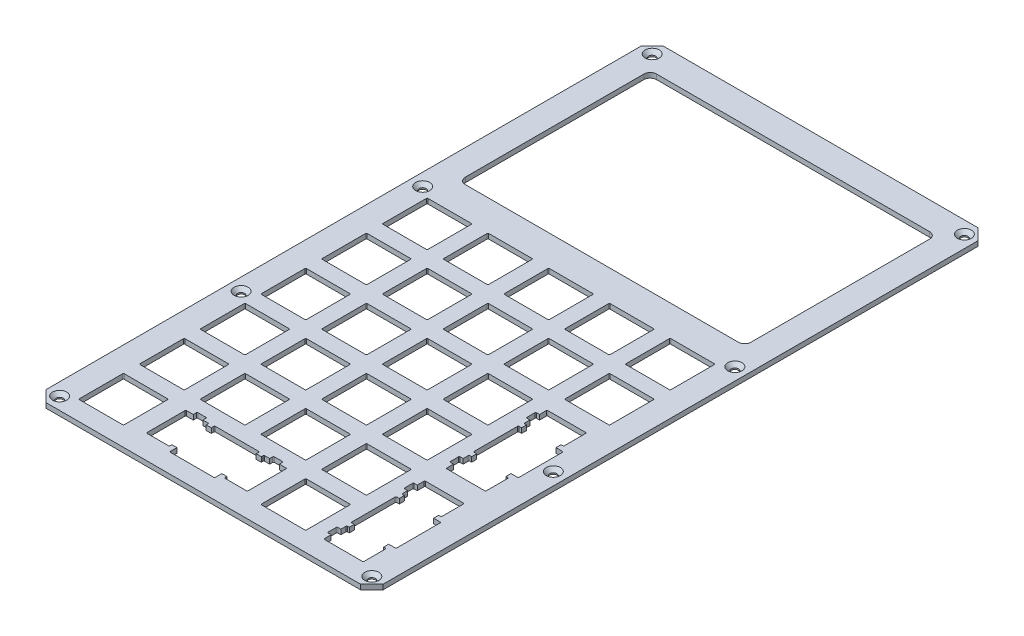
SolidWorks part; units mm, degrees
material "Brass"
ref_plane "Front Plane" through (0, 0, 0) normal (0, 0, 1) x (1, 0, 0)
ref_plane "Top Plane" through (0, 0, 0) normal (0, 1, 0) x (1, 0, 0)
ref_plane "Right Plane" through (0, 0, 0) normal (1, 0, 0) x (0, 0, -1)
sketch "Sketch1" plane through (0, 0, 0) normal (0, 1, 0) x (1, 0, 0)
  line L0 (25.9207, -6.9977) -> (25.9207, 6.9977)
  line L1 (6.9977, -6.9977) -> (-6.9977, -6.9977)
  line L2 (6.9977, -6.9977) -> (6.9977, 6.9977)
  line L3 (6.9977, 6.9977) -> (-6.9977, 6.9977)
  line L4 (-6.9977, -6.9977) -> (-6.9977, 6.9977)
  line L5 (6.9977, -6.9977) -> (-6.9977, 6.9977) construction
  line L6 (6.9977, 6.9977) -> (-6.9977, -6.9977) construction
  line L7 (25.9207, -6.9977) -> (11.9253, -6.9977)
  line L8 (11.9253, -6.9977) -> (11.9253, 6.9977)
  line L9 (25.9207, 6.9977) -> (11.9253, 6.9977)
  line L10 (44.8437, -6.9977) -> (44.8437, 6.9977)
  line L11 (44.8437, -6.9977) -> (30.8483, -6.9977)
  line L12 (30.8483, -6.9977) -> (30.8483, 6.9977)
  line L13 (44.8437, 6.9977) -> (30.8483, 6.9977)
  line L14 (63.7667, -6.9977) -> (63.7667, 6.9977)
  line L15 (63.7667, -6.9977) -> (49.7713, -6.9977)
  line L16 (49.7713, -6.9977) -> (49.7713, 6.9977)
  line L17 (63.7667, 6.9977) -> (49.7713, 6.9977)
  line L18 (82.6897, -6.9977) -> (82.6897, 6.9977)
  line L19 (82.6897, -6.9977) -> (68.6943, -6.9977)
  line L20 (68.6943, -6.9977) -> (68.6943, 6.9977)
  line L21 (82.6897, 6.9977) -> (68.6943, 6.9977)
  line L22 (25.9207, -25.9207) -> (25.9207, -11.9253)
  line L23 (25.9207, -25.9207) -> (11.9253, -25.9207)
  line L24 (11.9253, -25.9207) -> (11.9253, -11.9253)
  line L25 (25.9207, -11.9253) -> (11.9253, -11.9253)
  line L26 (44.8437, -25.9207) -> (44.8437, -11.9253)
  line L27 (44.8437, -25.9207) -> (30.8483, -25.9207)
  line L28 (30.8483, -25.9207) -> (30.8483, -11.9253)
  line L29 (44.8437, -11.9253) -> (30.8483, -11.9253)
  line L30 (63.7667, -25.9207) -> (63.7667, -11.9253)
  line L31 (63.7667, -25.9207) -> (49.7713, -25.9207)
  line L32 (49.7713, -25.9207) -> (49.7713, -11.9253)
  line L33 (63.7667, -11.9253) -> (49.7713, -11.9253)
  line L34 (82.6897, -25.9207) -> (82.6897, -11.9253)
  line L35 (82.6897, -25.9207) -> (68.6943, -25.9207)
  line L36 (68.6943, -25.9207) -> (68.6943, -11.9253)
  line L37 (82.6897, -11.9253) -> (68.6943, -11.9253)
  line L38 (25.9207, -44.8437) -> (25.9207, -30.8483)
  line L39 (25.9207, -44.8437) -> (11.9253, -44.8437)
  line L40 (11.9253, -44.8437) -> (11.9253, -30.8483)
  line L41 (25.9207, -30.8483) -> (11.9253, -30.8483)
  line L42 (44.8437, -44.8437) -> (44.8437, -30.8483)
  line L43 (44.8437, -44.8437) -> (30.8483, -44.8437)
  line L44 (30.8483, -44.8437) -> (30.8483, -30.8483)
  line L45 (44.8437, -30.8483) -> (30.8483, -30.8483)
  line L46 (63.7667, -44.8437) -> (63.7667, -30.8483)
  line L47 (63.7667, -44.8437) -> (49.7713, -44.8437)
  line L48 (49.7713, -44.8437) -> (49.7713, -30.8483)
  line L49 (63.7667, -30.8483) -> (49.7713, -30.8483)
  line L50 (82.6897, -44.8437) -> (82.6897, -30.8483) [skipped]
  line L51 (82.6897, -44.8437) -> (68.6943, -44.8437) [skipped]
  line L52 (68.6943, -44.8437) -> (68.6943, -30.8483) [skipped]
  line L53 (82.6897, -30.8483) -> (68.6943, -30.8483) [skipped]
  line L54 (25.9207, -63.7667) -> (25.9207, -49.7713)
  line L55 (25.9207, -63.7667) -> (11.9253, -63.7667)
  line L56 (11.9253, -63.7667) -> (11.9253, -49.7713)
  line L57 (25.9207, -49.7713) -> (11.9253, -49.7713)
  line L58 (44.8437, -63.7667) -> (44.8437, -49.7713)
  line L59 (44.8437, -63.7667) -> (30.8483, -63.7667)
  line L60 (30.8483, -63.7667) -> (30.8483, -49.7713)
  line L61 (44.8437, -49.7713) -> (30.8483, -49.7713)
  line L62 (63.7667, -63.7667) -> (63.7667, -49.7713)
  line L63 (63.7667, -63.7667) -> (49.7713, -63.7667)
  line L64 (49.7713, -63.7667) -> (49.7713, -49.7713)
  line L65 (63.7667, -49.7713) -> (49.7713, -49.7713)
  line L66 (82.6897, -63.7667) -> (82.6897, -49.7713) [skipped]
  line L67 (82.6897, -63.7667) -> (68.6943, -63.7667) [skipped]
  line L68 (68.6943, -63.7667) -> (68.6943, -49.7713) [skipped]
  line L69 (82.6897, -49.7713) -> (68.6943, -49.7713) [skipped]
  line L70 (25.9207, -82.6897) -> (25.9207, -68.6943)
  line L71 (25.9207, -82.6897) -> (11.9253, -82.6897)
  line L72 (11.9253, -82.6897) -> (11.9253, -68.6943)
  line L73 (25.9207, -68.6943) -> (11.9253, -68.6943)
  line L74 (44.8437, -82.6897) -> (44.8437, -68.6943)
  line L75 (44.8437, -82.6897) -> (30.8483, -82.6897)
  line L76 (30.8483, -82.6897) -> (30.8483, -68.6943)
  line L77 (44.8437, -68.6943) -> (30.8483, -68.6943)
  line L78 (63.7667, -82.6897) -> (63.7667, -68.6943)
  line L79 (63.7667, -82.6897) -> (49.7713, -82.6897)
  line L80 (49.7713, -82.6897) -> (49.7713, -68.6943)
  line L81 (63.7667, -68.6943) -> (49.7713, -68.6943)
  line L82 (82.6897, -82.6897) -> (82.6897, -68.6943) [skipped]
  line L83 (82.6897, -82.6897) -> (68.6943, -82.6897) [skipped]
  line L84 (68.6943, -82.6897) -> (68.6943, -68.6943) [skipped]
  line L85 (82.6897, -68.6943) -> (68.6943, -68.6943) [skipped]
  line L86 (25.9207, -101.6127) -> (25.9207, -87.6173) [skipped]
  line L87 (25.9207, -101.6127) -> (11.9253, -101.6127) [skipped]
  line L88 (11.9253, -101.6127) -> (11.9253, -87.6173) [skipped]
  line L89 (25.9207, -87.6173) -> (11.9253, -87.6173) [skipped]
  line L90 (44.8437, -101.6127) -> (44.8437, -87.6173) [skipped]
  line L91 (44.8437, -101.6127) -> (30.8483, -101.6127) [skipped]
  line L92 (30.8483, -101.6127) -> (30.8483, -87.6173) [skipped]
  line L93 (44.8437, -87.6173) -> (30.8483, -87.6173) [skipped]
  line L94 (63.7667, -101.6127) -> (63.7667, -87.6173)
  line L95 (63.7667, -101.6127) -> (49.7713, -101.6127)
  line L96 (49.7713, -101.6127) -> (49.7713, -87.6173)
  line L97 (63.7667, -87.6173) -> (49.7713, -87.6173)
  line L98 (82.6897, -101.6127) -> (82.6897, -87.6173) [skipped]
  line L99 (82.6897, -101.6127) -> (68.6943, -101.6127) [skipped]
  line L100 (68.6943, -101.6127) -> (68.6943, -87.6173) [skipped]
  line L101 (82.6897, -87.6173) -> (68.6943, -87.6173) [skipped]
  line L102 (6.9977, -25.9207) -> (6.9977, -11.9253)
  line L103 (6.9977, -25.9207) -> (-6.9977, -25.9207)
  line L104 (-6.9977, -25.9207) -> (-6.9977, -11.9253)
  line L105 (6.9977, -11.9253) -> (-6.9977, -11.9253)
  line L106 (6.9977, -44.8437) -> (6.9977, -30.8483)
  line L107 (6.9977, -44.8437) -> (-6.9977, -44.8437)
  line L108 (-6.9977, -44.8437) -> (-6.9977, -30.8483)
  line L109 (6.9977, -30.8483) -> (-6.9977, -30.8483)
  line L110 (6.9977, -63.7667) -> (6.9977, -49.7713)
  line L111 (6.9977, -63.7667) -> (-6.9977, -63.7667)
  line L112 (-6.9977, -63.7667) -> (-6.9977, -49.7713)
  line L113 (6.9977, -49.7713) -> (-6.9977, -49.7713)
  line L114 (6.9977, -82.6897) -> (6.9977, -68.6943)
  line L115 (6.9977, -82.6897) -> (-6.9977, -82.6897)
  line L116 (-6.9977, -82.6897) -> (-6.9977, -68.6943)
  line L117 (6.9977, -68.6943) -> (-6.9977, -68.6943)
  line L118 (6.9977, -101.6127) -> (6.9977, -87.6173)
  line L119 (6.9977, -101.6127) -> (-6.9977, -101.6127)
  line L120 (-6.9977, -101.6127) -> (-6.9977, -87.6173)
  line L121 (6.9977, -87.6173) -> (-6.9977, -87.6173)
  line L122 (6.9977, -6.9977) -> (25.9207, -6.9977) construction
  line L123 (6.9977, -6.9977) -> (6.9977, -25.9207) construction
  line L124 (25.9207, -75.692) -> (30.8483, -75.692) construction
  line L125 (56.769, -44.8437) -> (56.769, -49.7713) construction
  line L126 (13.1595, -100.1473) -> (12.6515, -100.1473)
  line L127 (-14.654, 84.7537) -> (90.346, 84.7537)
  line L128 (-14.654, 84.7537) -> (-14.654, -107.5917)
  line L129 (-14.654, -107.5917) -> (90.346, -107.5917)
  line L130 (90.346, 84.7537) -> (90.346, -107.5917)
  line L131 (82.3656, 76.1637) -> (-6.6736, 76.1637)
  line L132 (82.3656, 76.1637) -> (82.3656, 16.5377)
  line L133 (82.3656, 16.5377) -> (-6.6736, 16.5377)
  line L134 (-6.6736, 76.1637) -> (-6.6736, 16.5377)
  line L135 (82.3656, 76.1637) -> (-6.6736, 16.5377) construction
  line L136 (82.3656, 16.5377) -> (-6.6736, 76.1637) construction
  line L137 (12.6515, -100.1473) -> (12.6515, -87.8473)
  line L138 (12.6515, -87.8473) -> (13.1595, -87.8473)
  line L139 (43.6095, -87.8473) -> (44.1175, -87.8473)
  line L140 (44.1175, -87.8473) -> (44.1175, -100.1473)
  line L141 (44.1175, -100.1473) -> (43.6095, -100.1473)
  line L142 (68.9243, -100.6325) -> (68.9243, -101.1405)
  line L143 (68.9243, -101.1405) -> (81.2243, -101.1405)
  line L144 (81.2243, -101.1405) -> (81.2243, -100.6325)
  line L145 (68.9243, -70.1825) -> (68.9243, -69.6745)
  line L146 (68.9243, -69.6745) -> (81.2243, -69.6745)
  line L147 (81.2243, -69.6745) -> (81.2243, -70.1825)
  line L148 (68.9243, -62.5325) -> (68.9243, -63.0405)
  line L149 (68.9243, -63.0405) -> (81.2243, -63.0405)
  line L150 (81.2243, -63.0405) -> (81.2243, -62.5325)
  line L151 (68.9243, -32.0825) -> (68.9243, -31.5745)
  line L152 (68.9243, -31.5745) -> (81.2243, -31.5745)
  line L153 (81.2243, -31.5745) -> (81.2243, -32.0825)
  line L155 (80.3656, 74.1637) -> (-4.6736, 74.1637) construction
  line L156 (80.3656, 74.1637) -> (80.3656, 18.5377) construction
  line L157 (80.3656, 18.5377) -> (-4.6736, 18.5377) construction
  line L158 (-4.6736, 74.1637) -> (-4.6736, 18.5377) construction
  line L159 (80.3656, 74.1637) -> (-4.6736, 18.5377) construction
  line L160 (80.3656, 18.5377) -> (-4.6736, 74.1637) construction
  arc A0 (82.3656, 74.1637) -> (80.3656, 76.1637) centre (80.3656, 74.1637) ccw
  arc A1 (80.3656, 16.5377) -> (82.3656, 18.5377) centre (80.3656, 18.5377) ccw
  arc A2 (-6.6736, 18.5377) -> (-4.6736, 16.5377) centre (-4.6736, 18.5377) ccw
  arc A3 (-4.6736, 76.1637) -> (-6.6736, 74.1637) centre (-4.6736, 74.1637) ccw
  circle A4 centre (0, -94.615) radius 2
  point P0 (0, 0)
  point P127 (28.3845, -75.692)
  point P130 (56.769, -47.3075)
  point P136 (37.846, 84.7537)
  point P137 (37.846, 46.3507)
  point P142 (37.846, 6.9977)
  point P166 (37.846, 46.3507)
  point P182 (6.9977, -94.615)
  point P184 (0, -87.6173)
  line B0 (68.6943, -40.3075) -> (68.6943, -54.3075)
  line B1 (68.6943, -54.3075) -> (69.7243, -54.3075)
  line B2 (69.7243, -54.3075) -> (69.7243, -55.8825)
  line B3 (69.7243, -55.8825) -> (68.9243, -55.8825)
  line B4 (68.9243, -55.8825) -> (68.9243, -57.7075)
  line B5 (68.9243, -57.7075) -> (67.7243, -57.7075)
  line B6 (67.7243, -57.7075) -> (67.7243, -60.7075)
  line B7 (67.7243, -60.7075) -> (68.9243, -60.7075)
  line B8 (68.9243, -60.7075) -> (68.9243, -62.5325)
  line B9 (68.9243, -62.5325) -> (75.1943, -62.5325)
  line B10 (77.9943, -62.5325) -> (81.2243, -62.5325)
  line B11 (81.2243, -62.5325) -> (81.2243, -55.8825)
  line B12 (81.2243, -55.8825) -> (80.4243, -55.8825)
  line B13 (80.4243, -55.8825) -> (80.4243, -54.3075)
  line B14 (80.4243, -54.3075) -> (82.6943, -54.3075)
  line B15 (82.6943, -54.3075) -> (82.6943, -40.3075)
  line B16 (82.6943, -47.3075) -> (68.6943, -47.3075) construction
  line B17 (80.4243, -40.3075) -> (82.6943, -40.3075)
  line B18 (80.4243, -38.7325) -> (80.4243, -40.3075)
  line B19 (81.2243, -38.7325) -> (80.4243, -38.7325)
  line B20 (81.2243, -32.0825) -> (81.2243, -38.7325)
  line B21 (77.9943, -32.0825) -> (81.2243, -32.0825)
  line B22 (68.9243, -32.0825) -> (75.1943, -32.0825)
  line B23 (68.9243, -33.9075) -> (68.9243, -32.0825)
  line B24 (67.7243, -33.9075) -> (68.9243, -33.9075)
  line B25 (67.7243, -36.9075) -> (67.7243, -33.9075)
  line B26 (68.9243, -36.9075) -> (67.7243, -36.9075)
  line B27 (68.9243, -38.7325) -> (68.9243, -36.9075)
  line B28 (69.7243, -38.7325) -> (68.9243, -38.7325)
  line B29 (69.7243, -40.3075) -> (69.7243, -38.7325)
  line B30 (68.6943, -40.3075) -> (69.7243, -40.3075)
  line B31 (75.1943, -62.5325) -> (77.9943, -62.5325)
  line B32 (75.1943, -32.0825) -> (77.9943, -32.0825)
  line B33 (68.6943, -78.4075) -> (68.6943, -92.4075)
  line B34 (68.6943, -92.4075) -> (69.7243, -92.4075)
  line B35 (69.7243, -92.4075) -> (69.7243, -93.9825)
  line B36 (69.7243, -93.9825) -> (68.9243, -93.9825)
  line B37 (68.9243, -93.9825) -> (68.9243, -95.8075)
  line B38 (68.9243, -95.8075) -> (67.7243, -95.8075)
  line B39 (67.7243, -95.8075) -> (67.7243, -98.8075)
  line B40 (67.7243, -98.8075) -> (68.9243, -98.8075)
  line B41 (68.9243, -98.8075) -> (68.9243, -100.6325)
  line B42 (68.9243, -100.6325) -> (75.1943, -100.6325)
  line B43 (77.9943, -100.6325) -> (81.2243, -100.6325)
  line B44 (81.2243, -100.6325) -> (81.2243, -93.9825)
  line B45 (81.2243, -93.9825) -> (80.4243, -93.9825)
  line B46 (80.4243, -93.9825) -> (80.4243, -92.4075)
  line B47 (80.4243, -92.4075) -> (82.6943, -92.4075)
  line B48 (82.6943, -92.4075) -> (82.6943, -78.4075)
  line B49 (82.6943, -85.4075) -> (68.6943, -85.4075) construction
  line B50 (80.4243, -78.4075) -> (82.6943, -78.4075)
  line B51 (80.4243, -76.8325) -> (80.4243, -78.4075)
  line B52 (81.2243, -76.8325) -> (80.4243, -76.8325)
  line B53 (81.2243, -70.1825) -> (81.2243, -76.8325)
  line B54 (77.9943, -70.1825) -> (81.2243, -70.1825)
  line B55 (68.9243, -70.1825) -> (75.1943, -70.1825)
  line B56 (68.9243, -72.0075) -> (68.9243, -70.1825)
  line B57 (67.7243, -72.0075) -> (68.9243, -72.0075)
  line B58 (67.7243, -75.0075) -> (67.7243, -72.0075)
  line B59 (68.9243, -75.0075) -> (67.7243, -75.0075)
  line B60 (68.9243, -76.8325) -> (68.9243, -75.0075)
  line B61 (69.7243, -76.8325) -> (68.9243, -76.8325)
  line B62 (69.7243, -78.4075) -> (69.7243, -76.8325)
  line B63 (68.6943, -78.4075) -> (69.7243, -78.4075)
  line B64 (75.1943, -100.6325) -> (77.9943, -100.6325)
  line B65 (75.1943, -70.1825) -> (77.9943, -70.1825)
  line B66 (35.3845, -87.6173) -> (21.3845, -87.6173)
  line B67 (21.3845, -87.6173) -> (21.3845, -88.6473)
  line B68 (21.3845, -88.6473) -> (19.8095, -88.6473)
  line B69 (19.8095, -88.6473) -> (19.8095, -87.8473)
  line B70 (19.8095, -87.8473) -> (17.9845, -87.8473)
  line B71 (17.9845, -87.8473) -> (17.9845, -86.6473)
  line B72 (17.9845, -86.6473) -> (14.9845, -86.6473)
  line B73 (14.9845, -86.6473) -> (14.9845, -87.8473)
  line B74 (14.9845, -87.8473) -> (13.1595, -87.8473)
  line B75 (13.1595, -87.8473) -> (13.1595, -94.1173)
  line B76 (13.1595, -96.9173) -> (13.1595, -100.1473)
  line B77 (13.1595, -100.1473) -> (19.8095, -100.1473)
  line B78 (19.8095, -100.1473) -> (19.8095, -99.3473)
  line B79 (19.8095, -99.3473) -> (21.3845, -99.3473)
  line B80 (21.3845, -99.3473) -> (21.3845, -101.6173)
  line B81 (21.3845, -101.6173) -> (35.3845, -101.6173)
  line B82 (28.3845, -101.6173) -> (28.3845, -87.6173) construction
  line B83 (35.3845, -99.3473) -> (35.3845, -101.6173)
  line B84 (36.9595, -99.3473) -> (35.3845, -99.3473)
  line B85 (36.9595, -100.1473) -> (36.9595, -99.3473)
  line B86 (43.6095, -100.1473) -> (36.9595, -100.1473)
  line B87 (43.6095, -96.9173) -> (43.6095, -100.1473)
  line B88 (43.6095, -87.8473) -> (43.6095, -94.1173)
  line B89 (41.7845, -87.8473) -> (43.6095, -87.8473)
  line B90 (41.7845, -86.6473) -> (41.7845, -87.8473)
  line B91 (38.7845, -86.6473) -> (41.7845, -86.6473)
  line B92 (38.7845, -87.8473) -> (38.7845, -86.6473)
  line B93 (36.9595, -87.8473) -> (38.7845, -87.8473)
  line B94 (36.9595, -88.6473) -> (36.9595, -87.8473)
  line B95 (35.3845, -88.6473) -> (36.9595, -88.6473)
  line B96 (35.3845, -87.6173) -> (35.3845, -88.6473)
  line B97 (13.1595, -94.1173) -> (13.1595, -96.9173)
  line B98 (43.6095, -94.1173) -> (43.6095, -96.9173)
  dimension "D16" = 4
  dimension "D1" = 13.9954
  dimension "D2" = 18.923
  dimension "D3" = 18.923
  dimension "D6" = 38.1
  dimension "D7" = 5.979
  dimension "D8" = 105
  dimension "D9" = 9.54
  dimension "D10" = 8.59
  dimension "D11" = 2
  dimension "D12" = 2
  dimension "D13" = 0.508
  dimension "D14" = 85.0392
  dimension "D15" = 55.626
  dimension "D4" = 5
  dimension "D5" = 6
sketch_block_instance "Metal Plate Stabilizer Cutout-1"
sketch_block "Metal Plate Stabilizer Cutout" parameters "D1"=14, "D2"=17.15, "D3"=20.8, "D4"=26.8, "D5"=30.45
sketch_block_instance "Metal Plate Stabilizer Cutout-2"
sketch_block_instance "Metal Plate Stabilizer Cutout-3"
extrude "Boss-Extrude1" add sketch "Sketch1" along normal blind 1.524 contours L130 L127 L128 L129 L134 L131 L132 L133 L121 L118 L119 L120 L117 L114 L115 L116 L113 L110 L111 L112 L109 L106 L107 L108 L105 L102 L103 L104 L97 L94 L95 L96 L81 L78 L79 L80 L77 L74 L75 L76 L73 | A2 L134 L133 | A3 L131 L134 | A0 L132 L131 | A1 L133 L132
fillet "Fillet1" radius 0.25 50 edges at (41.7845, 0.762, 86.6473) (36.9595, 0.762, 100.1473) (19.8095, 0.762, 100.1473) (14.9845, 0.762, 86.6473) (68.6943, 0.762, 92.4075) (68.6943, 0.762, 78.4075) (68.9243, 0.762, 76.8325) (81.2243, 0.762, 76.8325) (82.6943, 0.762, 92.4075) (67.7243, 0.762, 98.8075) (81.2243, 0.762, 38.7325) (81.2243, 0.762, 55.8825) (67.7243, 0.762, 57.7075) (6.9977, 0.762, 68.6943) (6.9977, 0.762, 82.6897) (-6.9977, 0.762, 68.6943) (-6.9977, 0.762, 49.7713) (6.9977, 0.762, 44.8437) (-6.9977, 0.762, 30.8483) (-6.9977, 0.762, 11.9253) (49.7713, 0.762, 101.6127) (49.7713, 0.762, 82.6897) (49.7713, 0.762, 68.6943) (25.9207, 0.762, 82.6897) (11.9253, 0.762, 82.6897) (63.7667, 0.762, 49.7713) (49.7713, 0.762, 49.7713) (30.8483, 0.762, 49.7713) (25.9207, 0.762, 63.7667) (49.7713, 0.762, 44.8437) (49.7713, 0.762, 30.8483) (11.9253, 0.762, 30.8483) (82.6897, 0.762, 25.9207) (68.6943, 0.762, 25.9207) (63.7667, 0.762, 11.9253) (63.7667, 0.762, 25.9207) (49.7713, 0.762, 11.9253) (44.8437, 0.762, 11.9253) (44.8437, 0.762, 25.9207) (30.8483, 0.762, 25.9207) (11.9253, 0.762, 11.9253) (63.7667, 0.762, -6.9977) (63.7667, 0.762, 6.9977) (44.8437, 0.762, 6.9977) (30.8483, 0.762, 6.9977) (81.2243, 0.762, 63.0405) (68.9243, 0.762, 31.5745) (68.9243, 0.762, 69.6745) (12.6515, 0.762, 100.1473) (44.1175, 0.762, 100.1473)
chamfer "Chamfer1" distance 3.5 angle 45 4 edges at (90.346, 0.762, 107.5917) (-14.654, 0.762, 107.5917) (90.346, 0.762, -84.7537) (-14.654, 0.762, -84.7537)
sketch "Sketch3" plane through (0, 1.524, 0) normal (0, 1, 0) x (1, 0, 0)
  circle A0 centre (-10.7827, 9.3824) radius 1.1 construction
  circle A1 centre (-10.7827, 9.3824) radius 1.1
  circle A2 centre (86.4747, -103.7204) radius 1.1 construction
  circle A3 centre (-10.7827, -103.7204) radius 1.1 construction
  circle A4 centre (-10.7827, -47.169) radius 1.1 construction
  circle A5 centre (-10.7827, 80.8824) radius 1.1 construction
  circle A6 centre (86.4747, -103.7204) radius 1.1
  circle A7 centre (-10.7827, -103.7204) radius 1.1
  circle A8 centre (-10.7827, -47.169) radius 1.1
  circle A9 centre (-10.7827, 80.8824) radius 1.1
  circle A10 centre (86.4747, 80.8824) radius 1.1 construction
  circle A11 centre (86.4747, 9.3824) radius 1.1 construction
  circle A12 centre (86.4747, -47.169) radius 1.1 construction
  circle A13 centre (86.4747, 80.8824) radius 1.1
  circle A14 centre (86.4747, 9.3824) radius 1.1
  circle A15 centre (86.4747, -47.169) radius 1.1
extrude "Cut-Extrude1" cut sketch "Sketch3" against normal through all
chamfer "Chamfer2" distance 1.1 angle 45 8 edges at (-10.7827, 1.524, -79.7824) (86.4747, 1.524, -8.2824) (86.4747, 1.524, 48.269) (86.4747, 1.524, 104.8204) (-10.7827, 1.524, 104.8204) (-10.7827, 1.524, 48.269) (-10.7827, 1.524, -8.2824) (86.4747, 1.524, -79.7824)
sketch "Sketch4" plane through (0, 1.524, 0) normal (0, 1, 0) x (1, 0, 0)
  line L0 (80.3656, 76.1637) -> (-4.6736, 76.1637) construction
  line L1 (82.3656, 74.1637) -> (82.3656, 18.5377) construction
  line L2 (80.3656, 16.5377) -> (-4.6736, 16.5377) construction
  line L3 (-6.6736, 74.1637) -> (-6.6736, 18.5377) construction
  line L4 (80.3656, 76.1637) -> (-4.6736, 76.1637)
  line L5 (82.3656, 74.1637) -> (82.3656, 18.5377)
  line L6 (80.3656, 16.5377) -> (-4.6736, 16.5377)
  line L7 (-6.6736, 74.1637) -> (-6.6736, 18.5377)
  line L8 (79.3656, 73.1637) -> (-3.6736, 73.1637)
  line L9 (-3.6736, 73.1637) -> (-3.6736, 19.5377)
  line L10 (79.3656, 19.5377) -> (-3.6736, 19.5377)
  line L11 (79.3656, 73.1637) -> (79.3656, 19.5377)
  arc A0 (-4.6736, 76.1637) -> (-6.6736, 74.1637) centre (-4.6736, 74.1637) ccw construction
  arc A1 (82.3656, 74.1637) -> (80.3656, 76.1637) centre (80.3656, 74.1637) ccw construction
  arc A2 (80.3656, 16.5377) -> (82.3656, 18.5377) centre (80.3656, 18.5377) ccw construction
  arc A3 (-6.6736, 18.5377) -> (-4.6736, 16.5377) centre (-4.6736, 18.5377) ccw construction
  arc A4 (-4.6736, 76.1637) -> (-6.6736, 74.1637) centre (-4.6736, 74.1637) ccw
  arc A5 (82.3656, 74.1637) -> (80.3656, 76.1637) centre (80.3656, 74.1637) ccw
  arc A6 (80.3656, 16.5377) -> (82.3656, 18.5377) centre (80.3656, 18.5377) ccw
  arc A7 (-6.6736, 18.5377) -> (-4.6736, 16.5377) centre (-4.6736, 18.5377) ccw
  arc A8 (-3.6736, 73.1637) -> (-3.6736, 73.1637) centre (-3.6736, 73.1637) ccw
  arc A9 (-3.6736, 19.5377) -> (-3.6736, 19.5377) centre (-3.6736, 19.5377) ccw
  arc A10 (79.3656, 19.5377) -> (79.3656, 19.5377) centre (79.3656, 19.5377) ccw
  arc A11 (79.3656, 73.1637) -> (79.3656, 73.1637) centre (79.3656, 73.1637) ccw
  point P24 (-3.6736, 19.5377)
  dimension "D1" = 3
